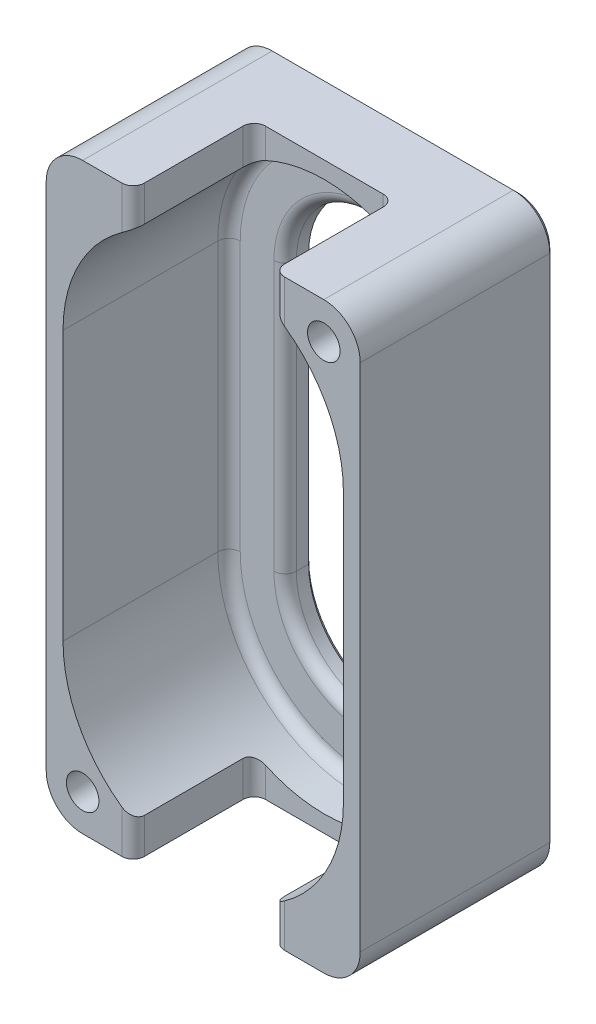
SolidWorks part; units mm, degrees
ref_plane "Front Plane" through (0, 0, 0) normal (0, 0, 1) x (1, 0, 0)
ref_plane "Top Plane" through (0, 0, 0) normal (0, 1, 0) x (1, 0, 0)
ref_plane "Right Plane" through (0, 0, 0) normal (1, 0, 0) x (0, 0, -1)
sketch "Sketch1" plane through (0, 0, 0) normal (0, 0, 1) x (1, 0, 0)
  line L0 (0, 24) -> (0, -24) construction
  line L1 (25, 24) -> (25, -24)
  line L2 (-25, 24) -> (-25, -24)
  line L4 (-28, -52) -> (28, -52)
  line L5 (-28, -52) -> (-28, 52)
  line L6 (-28, 52) -> (28, 52)
  line L7 (28, -52) -> (28, 52)
  line L8 (-28, -52) -> (28, 52) construction
  line L9 (-28, 52) -> (28, -52) construction
  arc A0 (25, 24) -> (-25, 24) centre (0, 24) ccw
  arc A1 (-25, -24) -> (25, -24) centre (0, -24) ccw
  point P3 (0, 0)
  point P8 (0, -49)
  point P9 (0, 49)
  point P10 (0, 0)
  dimension "D1" = 50
  dimension "D2" = 98
  dimension "D3" = 3
  dimension "D4" = 3
extrude "Boss-Extrude1" add sketch "Sketch1" along normal blind 29.6
sketch "Sketch2" plane through (0, 0, 0) normal (0, 0, -1) x (-1, 0, 0)
  line L4 (-28, 52) -> (-28, -52)
  line L5 (-28, -52) -> (28, -52)
  line L6 (28, -52) -> (28, 52)
  line L7 (28, 52) -> (-28, 52)
  line L8 (-28, 52) -> (-28, -52)
  line L9 (-28, -52) -> (28, -52)
  line L10 (28, -52) -> (28, 52)
  line L11 (28, 52) -> (-28, 52)
  line L14 (-15, 24) -> (-15, -24)
  line L15 (15, -24) -> (15, 24)
  line L16 (-15, 24) -> (-15, -24)
  line L17 (15, -24) -> (15, 24)
  arc A8 (-15, -24) -> (15, -24) centre (0, -24) ccw
  arc A9 (15, 24) -> (-15, 24) centre (0, 24) ccw
  arc A10 (-15, -24) -> (15, -24) centre (0, -24) ccw
  arc A11 (15, 24) -> (-15, 24) centre (0, 24) ccw
  dimension "D1" = 0
  dimension "D2" = 10
extrude "Boss-Extrude2" add sketch "Sketch2" along normal blind 5
fillet "Fillet1" radius 2 8 edges at (-15, 0, 0) (0, -39, 0) (15, 0, 0) (25, 0, 0) (0, -49, 0) (-25, 0, 0) (0, 39, 0) (0, 49, 0)
sketch "Sketch3" plane through (0, 0, 0) normal (0, 1, 0) x (1, 0, 0)
  line L0 (0, 0) -> (0, -8) construction
  line L1 (28, -29.6) -> (-28, -29.6) construction
  line L2 (-12.5, -29.6) -> (12.5, -29.6)
  line L3 (-12.5, -29.6) -> (-12.5, -8)
  line L4 (-12.5, -8) -> (12.5, -8)
  line L5 (12.5, -29.6) -> (12.5, -8)
  point P10 (0, -8)
  dimension "D1" = 8
  dimension "D2" = 25
extrude "Cut-Extrude1" cut sketch "Sketch3" against normal through all both and the other way through all
fillet "Fillet2" radius 2 8 edges at (12.5, -48.8253, 29.6) (12.5, -48.8253, 8) (-12.5, -48.8253, 29.6) (-12.5, -48.8253, 8) (-12.5, 48.8253, 8) (-12.5, 48.8253, 29.6) (12.5, 48.8253, 29.6) (12.5, 48.8253, 8)
fillet "Fillet3" radius 6.5 4 edges at (-28, 52, 12.3) (-28, -52, 12.3) (28, 52, 12.3) (28, -52, 12.3)
sketch "Sketch4" plane through (0, 0, -5) normal (0, 0, -1) x (-1, 0, 0)
  point P0 (-21.5, 45.5)
  point P1 (21.5, -45.5)
  point P3 (21.5, 45.5)
  point P5 (-21.5, -45.5)
hole_wizard "CSK for M5 Flat Head Machine Screw1" positions "3DSketch1" profile "Sketch5" countersink size "M5" standard "ANSI Metric" end condition through all
sketch3d "3DSketch1"
  line L0 (21.5, 45.5, 29.6) -> (21.5, 45.5, -5) construction
  line L1 (-21.5, -45.5, 29.6) -> (-21.5, -45.5, -5) construction
  point P0 (21.5, 45.5, -5)
  point P4 (-21.5, -45.5, -5)
sketch "Sketch5" plane through (21.5, 45.5, -5) normal (1, 0, 0) x (0, 1, 0)
  line L0 (0, 0) -> (0, 34.6)
  line L1 (0, 34.6) -> (2.9, 34.6)
  line L2 (2.9, 34.6) -> (2.9, 2.3)
  line L3 (2.9, 2.3) -> (5.2, 0)
  line L5 (5.2, 0) -> (0, 0)
  line L6 (-2.9, 2.3) -> (-5.2, 0) construction
  line L11 (0, -6.35) -> (0, 107.95) construction
  dimension "Thru Hole Dia." = 5.8
  dimension "Thru Hole Depth" = 34.6
  dimension "Near C'Sink Dia." = 10.4
  dimension "Near C'Sink Angle" = 90
chamfer "Chamfer1" distance 0.8 angle 45 12 edges at (0, -39, -5) (-15, 0, -5) (15, 0, -5) (0, 39, -5) (-28, 0, -5) (-26.0962, 50.0962, -5) (-26.0962, -50.0962, -5) (0, 52, -5) (0, -52, -5) (26.0962, 50.0962, -5) (26.0962, -50.0962, -5) (28, 0, -5)
